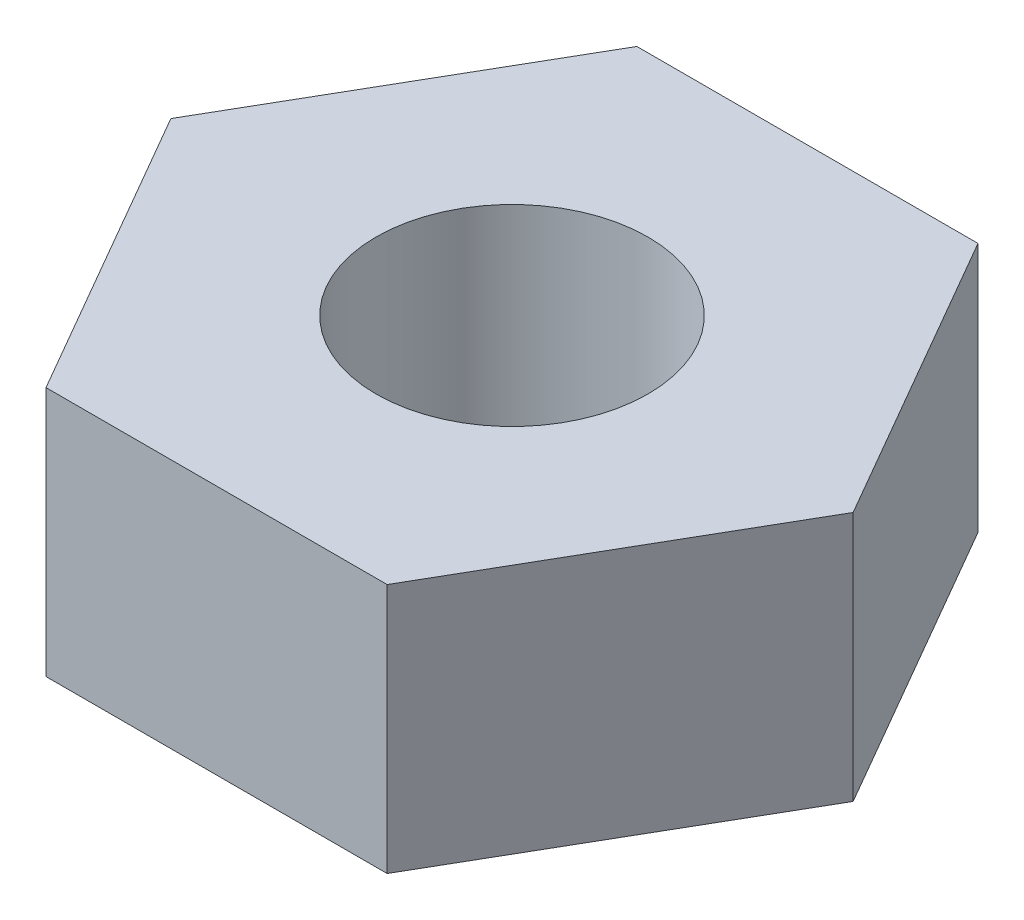
SolidWorks part; units mm, degrees
ref_plane "Front Plane" through (0, 0, 0) normal (0, 0, 1) x (1, 0, 0)
ref_plane "Top Plane" through (0, 0, 0) normal (0, 1, 0) x (1, 0, 0)
ref_plane "Right Plane" through (0, 0, 0) normal (1, 0, 0) x (0, 0, -1)
sketch "Sketch1" plane through (0, 0, 0) normal (0, 1, 0) x (1, 0, 0)
  line L1 (3.135, 0) -> (1.5675, 2.715)
  line L2 (1.5675, 2.715) -> (-1.5675, 2.715)
  line L3 (-1.5675, 2.715) -> (-3.135, 0)
  line L4 (-3.135, 0) -> (-1.5675, -2.715)
  line L5 (-1.5675, -2.715) -> (1.5675, -2.715)
  line L6 (1.5675, -2.715) -> (3.135, 0)
  circle A0 centre (0, 0) radius 2.715 construction
  circle A1 centre (0, 0) radius 1.25
  dimension "D2" = 2.5
  dimension "D1" = 5.43
extrude "Boss-Extrude1" add sketch "Sketch1" along normal blind 2.3
